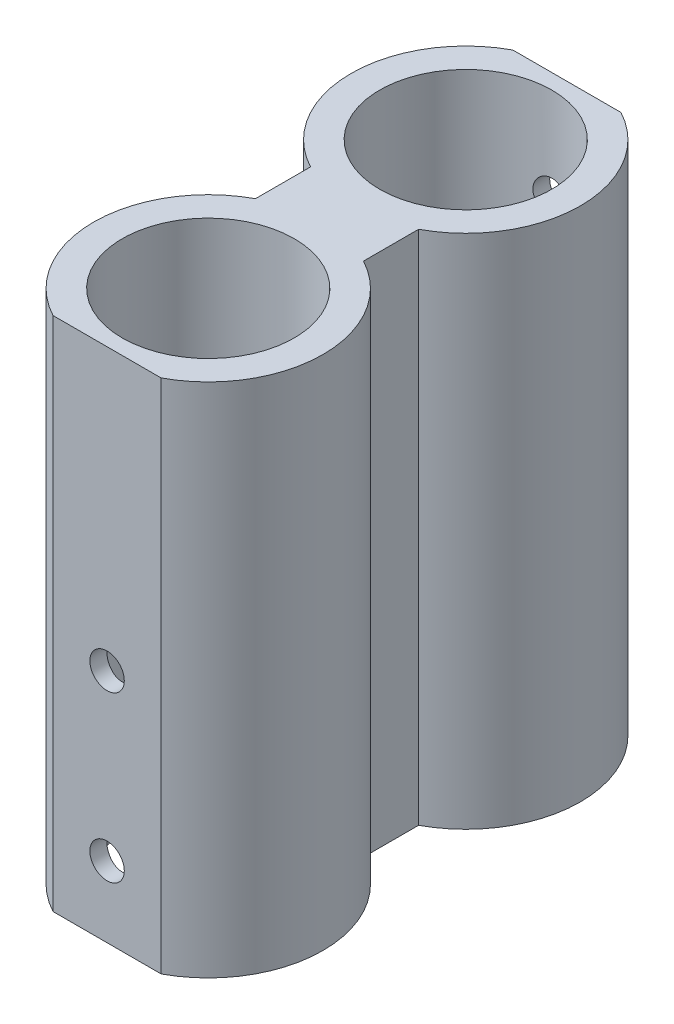
SolidWorks part; units mm, degrees
ref_plane "Front Plane" through (0, 0, 0) normal (0, 0, 1) x (1, 0, 0)
ref_plane "Top Plane" through (0, 0, 0) normal (0, 1, 0) x (1, 0, 0)
ref_plane "Right Plane" through (0, 0, 0) normal (1, 0, 0) x (0, 0, -1)
sketch "Sketch1" plane through (0, 0, 0) normal (0, 1, 0) x (1, 0, 0)
  line L0 (-4.7109, 8.8208) -> (4.7109, 8.8208)
  line L1 (4.7109, -8.8208) -> (4.7109, -13.6271)
  line L2 (-4.7109, -8.8208) -> (-4.7109, -13.6271)
  line L4 (-4.7109, -31.2687) -> (4.7109, -31.2687)
  arc A0 (4.7109, -8.8208) -> (4.7109, 8.8208) centre (0, 0) ccw
  arc A1 (-4.7109, -13.6271) -> (-4.7109, -31.2687) centre (0, -22.4479) ccw
  arc A2 (-4.7109, 8.8208) -> (-4.7109, -8.8208) centre (0, 0) ccw
  arc A3 (4.7109, -31.2687) -> (4.7109, -13.6271) centre (0, -22.4479) ccw
  point P11 (0, 8.8208)
  dimension "D1" = 20
extrude "Boss-Extrude2" add sketch "Sketch1" along normal blind 45
sketch "Sketch5" plane through (0, 45, 0) normal (0, 1, 0) x (1, 0, 0)
  circle A0 centre (0, 0) radius 7.5
  circle A1 centre (0, -22.4479) radius 7.5
  dimension "D1" = 15
  dimension "D2" = 15
extrude "Cut-Extrude2" cut sketch "Sketch5" against normal blind 48
sketch "Sketch6" plane through (0, 0, 31.2687) normal (0, 0, 1) x (1, 0, 0)
  circle A0 centre (0, 20.5327) radius 1.5
  circle A1 centre (0, 6.1789) radius 1.5
  dimension "D1" = 3
  dimension "D2" = 3
extrude "Cut-Extrude3" cut sketch "Sketch6" against normal blind 5
sketch "Sketch7" plane through (0, 0, -8.8208) normal (0, 0, -1) x (-1, 0, 0)
  line L0 (0, 45) -> (0, 0) construction
  line L1 (-4.7109, 45) -> (4.7109, 45) construction
  circle A0 centre (0, 36.8524) radius 1.5
  point P7 (0, 36.8524)
extrude "Cut-Extrude4" cut sketch "Sketch7" against normal blind 10
